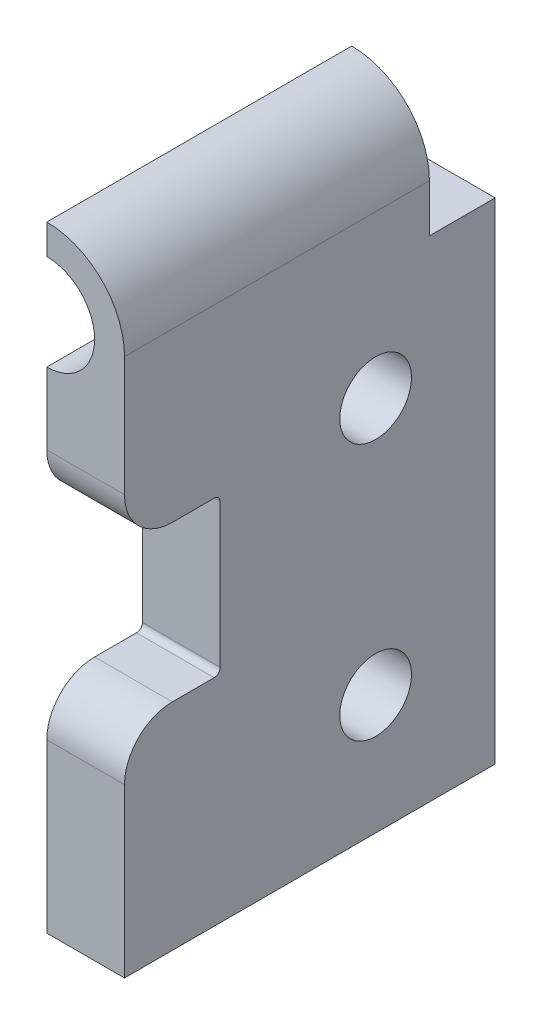
SolidWorks part; units mm, degrees
ref_plane "Front Plane" through (0, 0, 0) normal (0, 0, 1) x (1, 0, 0)
ref_plane "Top Plane" through (0, 0, 0) normal (0, 1, 0) x (1, 0, 0)
ref_plane "Right Plane" through (0, 0, 0) normal (1, 0, 0) x (0, 0, -1)
sketch "Sketch1" plane through (0, 0, 0) normal (0, 0, 1) x (1, 0, 0)
  line L0 (-3.75, 29) -> (-3.75, 22.5)
  line L2 (-3.75, 22.5) -> (-3.75, -22.5)
  line L3 (-3.75, -22.5) -> (2.75, -22.5)
  line L4 (2.75, 22.5) -> (2.75, -22.5)
  arc A0 (2.75, 22.5) -> (-3.75, 29) centre (-3.75, 22.5) ccw
  point P0 (0, 0)
  dimension "D1" = 6.5
  dimension "D2" = 45
extrude "Boss-Extrude1" add sketch "Sketch1" along normal blind 31
sketch "Sketch2" plane through (-3.75, 0, 0) normal (-1, 0, 0) x (0, 0, 1)
  line L1 (0, 29) -> (5.5, 29)
  line L2 (0, 29) -> (0, 18.5)
  line L3 (0, 18.5) -> (5.5, 18.5)
  line L4 (5.5, 29) -> (5.5, 18.5)
  dimension "D1" = 5.5
  dimension "D2" = 10.5
extrude "Cut-Extrude1" cut sketch "Sketch2" against normal through all
sketch "Sketch3" plane through (-3.75, 0, 0) normal (-1, 0, 0) x (0, 0, 1)
  line L0 (31, 29) -> (5.5, 29) construction
  line L2 (0, 18.5) -> (0, -22.5) construction
  line L3 (31, -22.5) -> (0, -22.5) construction
  circle A0 centre (10, 9) radius 3
  circle A1 centre (10, -12.5) radius 3
  dimension "D1" = 6
  dimension "D2" = 20
  dimension "D4" = 10
  dimension "D5" = 10
extrude "Cut-Extrude2" cut sketch "Sketch3" against normal through all
sketch "Sketch4" plane through (0, 0, 5.5) normal (0, 0, -1) x (-1, 0, 0)
  line L1 (-2.75, 18.5) -> (3.75, 18.5) construction
  line L2 (3.75, 26.5) -> (3.75, 18.5)
  arc A0 (3.75, 18.5) -> (3.75, 26.5) centre (3.75, 22.5) cw
  dimension "D1" = 4
  dimension "D2" = 4
extrude "Cut-Extrude4" cut sketch "Sketch4" against normal through all
sketch "Sketch6" plane through (-3.75, 0, 0) normal (-1, 0, 0) x (0, 0, 1)
  line L0 (31, 18.5) -> (31, -22.5) construction
  line L1 (31, 8.5) -> (23, 8.5)
  line L2 (31, 8.5) -> (31, -4.5)
  line L3 (31, -4.5) -> (23, -4.5)
  line L4 (23, 8.5) -> (23, -4.5)
  line L5 (31, 18.5) -> (5.5, 18.5) construction
  dimension "D1" = 8
  dimension "D2" = 13
  dimension "D3" = 10
extrude "Cut-Extrude5" cut sketch "Sketch6" against normal up to next
fillet "Fillet1" radius 0.5 2 edges at (-0.5, -4.5, 23) (-0.5, 8.5, 23)
fillet "Fillet2" radius 4 2 edges at (-0.5, -4.5, 31) (-0.5, 8.5, 31)
